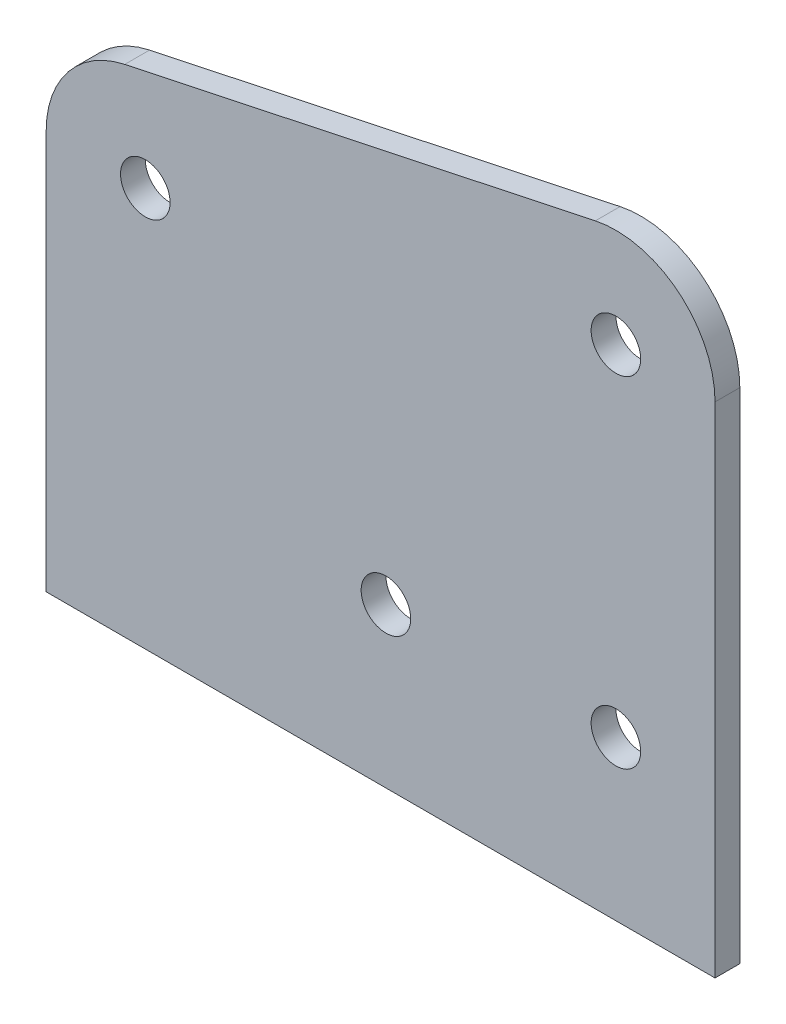
SolidWorks part; units mm, degrees
ref_plane "Front Plane" through (0, 0, 0) normal (0, 0, 1) x (1, 0, 0)
ref_plane "Top Plane" through (0, 0, 0) normal (0, 1, 0) x (1, 0, 0)
ref_plane "Right Plane" through (0, 0, 0) normal (1, 0, 0) x (0, 0, -1)
sketch "Sketch1" plane through (0, 0, 0) normal (0, 0, 1) x (1, 0, 0)
  line L0 (0, 0) -> (20.6877, 0) construction
  line L1 (20.6877, 0) -> (20.6877, 20.3568) construction
  line L2 (20.6877, 20.3568) -> (20.6877, 63.9178) construction
  line L3 (20.6877, 20.3568) -> (-8.7763, 20.3568) construction
  line L4 (-8.7763, 20.3568) -> (-39.6056, 20.3568) construction
  line L5 (-39.6056, 20.3568) -> (-39.6056, 51.1312) construction
  line L6 (18.0529, 76.3415) -> (-42.2403, 63.5549)
  line L7 (-52.3056, 51.1312) -> (-52.3056, 0)
  line L8 (33.3877, 63.9178) -> (33.3877, 0)
  line L9 (-52.3056, 0) -> (33.3877, 0)
  circle A0 centre (20.6877, 20.3568) radius 3.175
  circle A1 centre (20.6877, 63.9178) radius 3.175
  circle A2 centre (-8.7763, 20.3568) radius 3.175
  circle A3 centre (-39.6056, 51.1312) radius 3.175
  arc A4 (33.3877, 63.9178) -> (18.0529, 76.3415) centre (20.6877, 63.9178) ccw
  arc A5 (-42.2403, 63.5549) -> (-52.3056, 51.1312) centre (-39.6056, 51.1312) ccw
  dimension "D2" = 6.35
  dimension "D4" = 6.35
  dimension "D5" = 6.35
  dimension "D7" = 6.35
  dimension "D10" = 25.4
  dimension "D11" = 25.4
  dimension "D1" = 20.3568
  dimension "D3" = 43.561
  dimension "D6" = 29.464
  dimension "D8" = 30.8293
  dimension "D9" = 30.7744
extrude "Boss-Extrude1" add sketch "Sketch1" along normal blind 3.175
